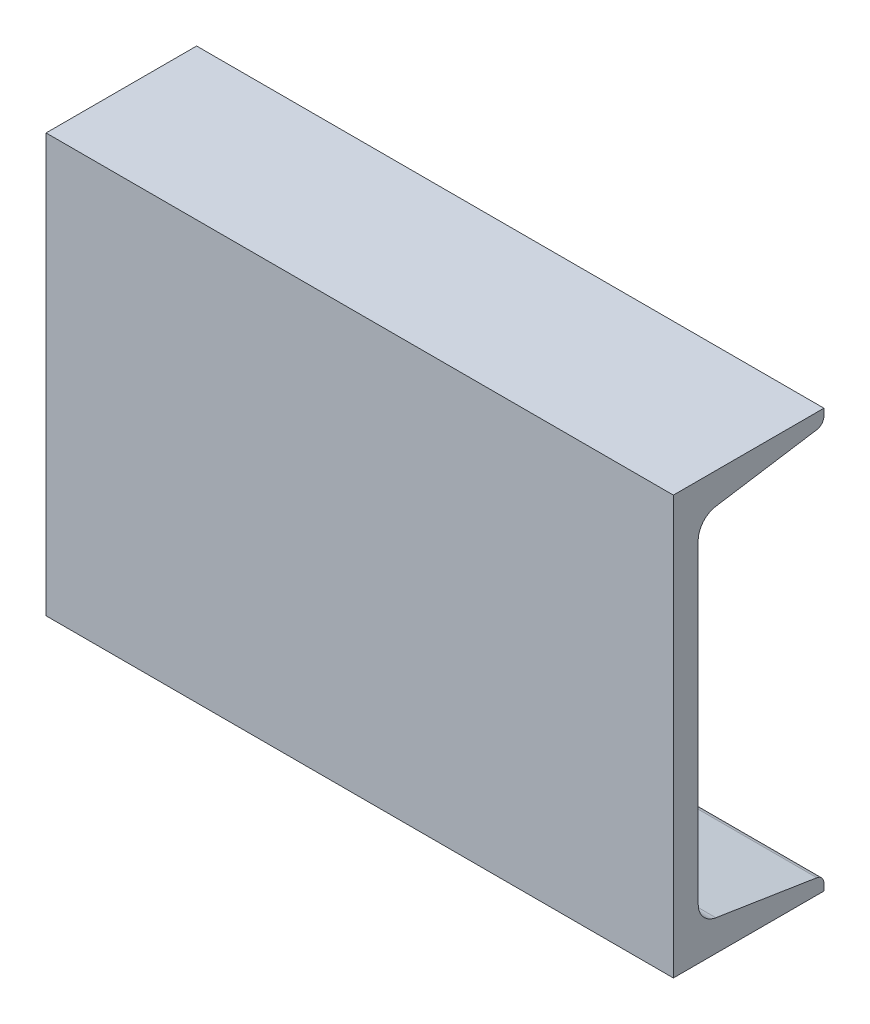
SolidWorks part; units mm, degrees
ref_plane "Front Plane" through (0, 0, 0) normal (0, 0, 1) x (1, 0, 0)
ref_plane "Top Plane" through (0, 0, 0) normal (0, 1, 0) x (1, 0, 0)
ref_plane "Right Plane" through (0, 0, 0) normal (1, 0, 0) x (0, 0, -1)
sketch "Sketch1" plane through (0, 0, 0) normal (1, 0, 0) x (0, 0, -1)
  line L0 (-25.3365, -76.2) -> (-25.3365, 76.2)
  line L1 (-25.3365, 76.2) -> (29.5275, 76.2)
  line L2 (-25.3365, -76.2) -> (29.5275, -76.2)
  line L3 (4.3561, -67.4878) -> (-21.0439, -67.4878) construction
  line L4 (-16.2941, 57.3918) -> (-16.2941, -57.3918)
  line L5 (29.5275, 76.2) -> (29.5275, 73.7107)
  line L6 (29.5275, -76.2) -> (29.5275, -73.7107)
  line L7 (-9.8562, 64.9196) -> (26.9523, 70.6996)
  line L8 (-9.8562, -64.9196) -> (26.9523, -70.6996)
  arc A0 (-16.2941, -57.3918) -> (-9.8562, -64.9196) centre (-8.6741, -57.3918) ccw
  arc A1 (-16.2941, 57.3918) -> (-9.8562, 64.9196) centre (-8.6741, 57.3918) cw
  arc A2 (29.5275, 73.7107) -> (26.9523, 70.6996) centre (26.4795, 73.7107) cw
  arc A3 (29.5275, -73.7107) -> (26.9523, -70.6996) centre (26.4795, -73.7107) ccw
  dimension "D1" = 9.0424
  dimension "D2" = 54.864
extrude "Boss-Extrude1" add sketch "Sketch1" along normal mid plane 228.6
